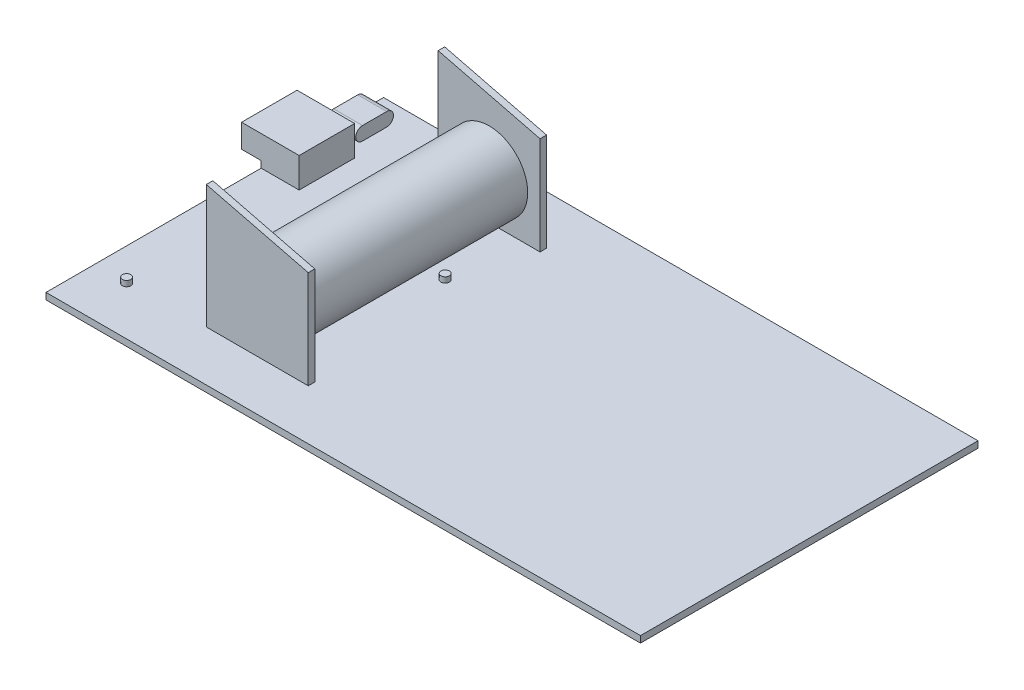
SolidWorks part; units mm, degrees
ref_plane "Front Plane" through (0, 0, 0) normal (0, 0, 1) x (1, 0, 0)
ref_plane "Top Plane" through (0, 0, 0) normal (0, 1, 0) x (1, 0, 0)
ref_plane "Right Plane" through (0, 0, 0) normal (1, 0, 0) x (0, 0, -1)
sketch "Sketch1" plane through (0, 0, 0) normal (0, 1, 0) x (1, 0, 0)
  line L1 (-70.45, -40) -> (70.45, -40)
  line L2 (-70.45, -40) -> (-70.45, 40)
  line L3 (-70.45, 40) -> (70.45, 40)
  line L4 (70.45, -40) -> (70.45, 40)
  line L5 (-70.45, -40) -> (70.45, 40) construction
  line L6 (-70.45, 40) -> (70.45, -40) construction
  point P0 (0, 0)
  dimension "D1" = 140.9
  dimension "D2" = 80
extrude "PCB" add sketch "Sketch1" along normal blind 1.55
sketch "Sketch3" plane through (-70.45, 0, 0) normal (-1, 0, 0) x (0, 0, 1)
  line L0 (-34.3, 3.15) -> (-28.56, 3.15) construction
  line L1 (-34.3, 4.75) -> (-28.56, 4.75)
  line L2 (-34.3, 1.55) -> (-28.56, 1.55)
  line L3 (-40, 0) -> (40, 0) construction
  line L4 (-40, 1.55) -> (-40, 0) construction
  line L5 (-40, 1.55) -> (40, 1.55) construction
  arc A0 (-34.3, 4.75) -> (-34.3, 1.55) centre (-34.3, 3.15) ccw
  arc A1 (-28.56, 1.55) -> (-28.56, 4.75) centre (-28.56, 3.15) ccw
  point P2 (-31.43, 3.15)
  dimension "D1" = 5.74
  dimension "D2" = 1.6
  dimension "D3" = 5.7
  dimension "D4" = 1.6
extrude "bodyC" add sketch "Sketch3" against normal blind 6.45 and the other way blind 0.4
sketch "Sketch4" plane through (0, 1.55, 0) normal (0, 1, 0) x (1, 0, 0)
  line L0 (70.45, 40) -> (-70.45, 40) construction
  line L1 (-61.45, 11) -> (-75.1, 11)
  line L2 (-61.45, 11) -> (-61.45, 24.15)
  line L3 (-61.45, 24.15) -> (-75.1, 24.15)
  line L4 (-75.1, 11) -> (-75.1, 24.15)
  line L6 (-70.45, 28.56) -> (-70.45, -40) construction
  dimension "D1" = 13.65
  dimension "D2" = 13.15
  dimension "D3" = 15.85
  dimension "D4" = 4.65
extrude "Boss-Extrude4" add sketch "Sketch4" along normal blind 7.1 and the other way blind 1.55
sketch "Sketch5" plane through (0, 0, -11) normal (0, 0, 1) x (1, 0, 0)
  line L0 (-75.1, 0) -> (-75.1, 8.65) construction
  line L1 (-70.45, 0) -> (-75.1, 0)
  line L2 (-70.45, 0) -> (-70.45, 3.1)
  line L3 (-70.45, 3.1) -> (-75.1, 3.1)
  line L4 (-75.1, 0) -> (-75.1, 3.1)
  dimension "D1" = 3.1
extrude "Cut-Extrude3" cut sketch "Sketch5" against normal blind 14.1
sketch "Sketch11" plane through (0, 1.55, 0) normal (0, 1, 0) x (1, 0, 0)
  line L1 (-44.35, 26.85) -> (-20.2, 26.85)
  line L2 (-44.35, 26.85) -> (-44.35, 28.4)
  line L3 (-44.35, 28.4) -> (-20.2, 28.4)
  line L4 (-20.2, 26.85) -> (-20.2, 28.4)
  line L6 (70.45, 40) -> (-70.45, 40) construction
  line L7 (-70.45, 40) -> (-70.45, 34.3) construction
  dimension "D1" = 11.6
  dimension "D2" = 26.1
  dimension "D3" = 1.55
  dimension "D4" = 24.15
extrude "Boss-Extrude8" add sketch "Sketch11" along normal blind 29.25
sketch "Sketch7" plane through (0, 1.55, 0) normal (0, 1, 0) x (1, 0, 0)
  line L0 (-70.45, 11) -> (-70.45, -40) construction
  line L1 (-44.35, -28.1) -> (-20.2, -28.1)
  line L2 (-44.35, -28.1) -> (-44.35, -26.55)
  line L3 (-44.35, -26.55) -> (-20.2, -26.55)
  line L4 (-20.2, -28.1) -> (-20.2, -26.55)
  line L5 (-70.45, -40) -> (70.45, -40) construction
  dimension "D1" = 26.1
  dimension "D2" = 11.9
  dimension "D3" = 1.55
  dimension "D4" = 24.15
extrude "Boss-Extrude5" add sketch "Sketch7" along normal blind 29.25
sketch "Sketch8" plane through (0, 0, 28.1) normal (0, 0, 1) x (1, 0, 0)
  line L0 (-44.35, 30.8) -> (-20.2, 24.7787)
  line L1 (-20.2, 30.8) -> (-20.2, 1.55) construction
  line L5 (-20.2, 30.8) -> (-44.35, 30.8)
  line L6 (-20.2, 24.7787) -> (-20.2, 30.8)
  dimension "D1" = 14
extrude "Cut-Extrude4" cut sketch "Sketch8" against normal blind 89
sketch "Sketch12" plane through (0, 0, -26.85) normal (0, 0, 1) x (1, 0, 0)
  line L0 (-32.275, 1.55) -> (-32.275, 12.25)
  line L1 (-44.35, 1.55) -> (-20.2, 1.55) construction
  circle A0 centre (-32.275, 12.25) radius 9.15
  dimension "D1" = 10.7
extrude "Battery" add sketch "Sketch12" along normal blind 54
sketch "Sketch13" plane through (0, 1.55, 0) normal (0, 1, 0) x (1, 0, 0)
  line L0 (-70.45, -28.6) -> (-62.75, -28.6)
  line L1 (-70.45, 11) -> (-70.45, -40) construction
  line L2 (-70.45, -40) -> (70.45, -40) construction
  circle A0 centre (-62.75, -28.6) radius 1
  dimension "D1" = 7.7
  dimension "D2" = 11.4
extrude "Button" add sketch "Sketch13" along normal blind 1.3 contours A0
sketch "Sketch14" plane through (0, 1.55, 0) normal (0, 1, 0) x (1, 0, 0)
  line L0 (-33.45, 9.9) -> (-25.75, 9.9)
  line L3 (70.45, 40) -> (-70.45, 40) construction
  line L4 (70.45, -40) -> (70.45, 40) construction
  circle A0 centre (-25.75, 9.9) radius 1
  dimension "D3" = 96.2
  dimension "D2" = 30.1
  dimension "D1" = 7.7
extrude "Reset" add sketch "Sketch14" along normal blind 1.3 contours A0
